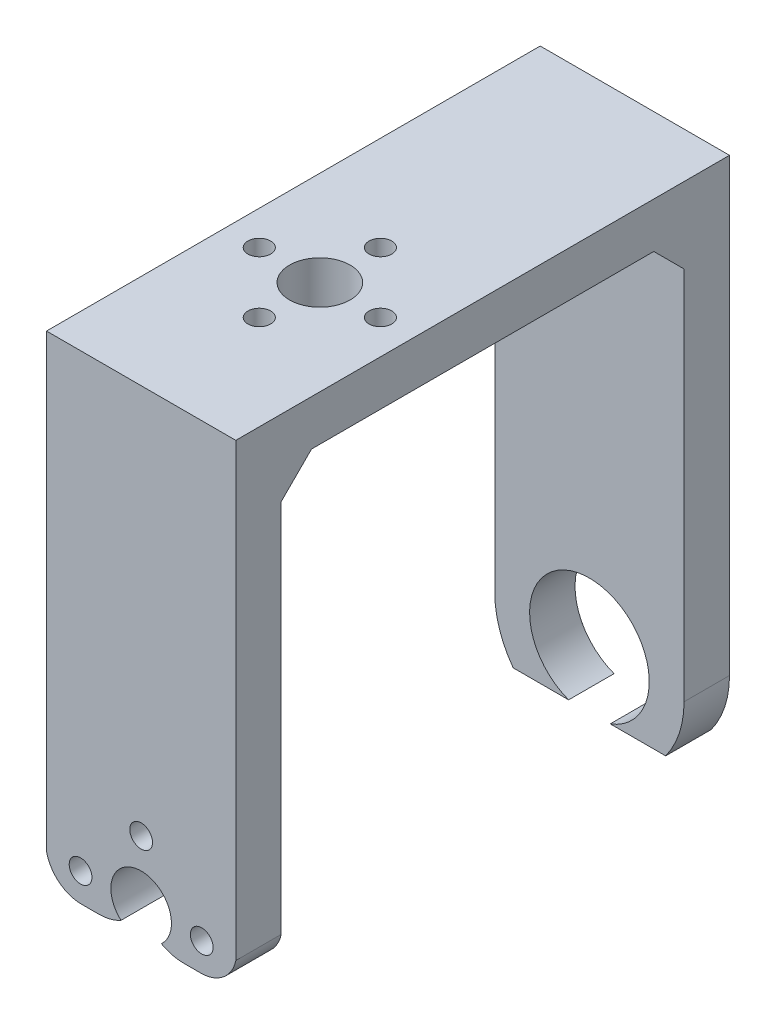
SolidWorks part; units mm, degrees
ref_plane "Alzado" through (0, 0, 0) normal (0, 0, 1) x (1, 0, 0)
ref_plane "Planta" through (0, 0, 0) normal (0, 1, 0) x (1, 0, 0)
ref_plane "Vista lateral" through (0, 0, 0) normal (1, 0, 0) x (0, 0, -1)
sketch "Croquis1" plane through (0, 0, 0) normal (1, 0, 0) x (0, 0, -1)
  line L0 (0, 49.6664) -> (0, -20.3336) construction
  line L1 (-26.6, -20.3336) -> (-26.6, 43.6664)
  line L2 (-26.6, 43.6664) -> (26.6, 43.6664)
  line L3 (-26.6, -20.3336) -> (-32.6, -20.3336)
  line L4 (-32.6, -20.3336) -> (-32.6, 49.6664)
  line L5 (-32.6, 49.6664) -> (32.6, 49.6664)
  line L6 (32.6, -20.3336) -> (32.6, 49.6664)
  line L7 (26.6, -20.3336) -> (32.6, -20.3336)
  line L8 (26.6, -20.3336) -> (26.6, 43.6664)
  point P9 (0, 43.6664)
  dimension "D1" = 53.2
  dimension "D2" = 6
  dimension "D3" = 6
  dimension "D4" = 70
extrude "Saliente-Extruir1" add sketch "Croquis1" along normal blind 25
sketch "Croquis3" plane through (0, 0, -32.6) normal (0, 0, -1) x (-1, 0, 0)
  line L0 (-12.5, -20.3336) -> (-12.5, 7.9911) construction
  line L1 (-25, -20.3336) -> (0, -20.3336) construction
  line L2 (-15.2463, -17.2409) -> (-22.5689, -17.2409)
  line L3 (-25, -20.3336) -> (-25, 49.6664) construction
  line L4 (-25, -9.8336) -> (-25, -20.3336)
  line L5 (-25, -20.3336) -> (0, -20.3336)
  line L6 (0, -9.8336) -> (0, -20.3336)
  line L7 (-9.7537, -17.2409) -> (-2.4311, -17.2409)
  arc A0 (-15.2463, -17.2409) -> (-9.7537, -17.2409) centre (-12.5, -9.8336) cw
  arc A1 (-22.5689, -17.2409) -> (-25, -9.8336) centre (-12.5, -9.8336) cw
  arc A2 (-2.4311, -17.2409) -> (0, -9.8336) centre (-12.5, -9.8336) ccw
  dimension "D2" = 7.9
  dimension "D1" = 10.5
extrude "Cortar-Extruir2" cut sketch "Croquis3" against normal up to next
sketch "Croquis4" plane through (0, 49.6664, 0) normal (0, 1, 0) x (1, 0, 0)
  line L0 (12.5, 32.6) -> (12.5, -32.6) construction
  line L1 (25, 32.6) -> (0, 32.6) construction
  line L2 (25, -32.6) -> (0, -32.6) construction
  line L3 (0, -9) -> (25, -9) construction
  circle A0 centre (12.5, -1) radius 1.5
  circle A1 centre (4.5, -9) radius 1.5
  circle A2 centre (12.5, -17) radius 1.5
  circle A3 centre (20.5, -9) radius 1.5
  circle A4 centre (12.5, -9) radius 4
  point P9 (12.5, 0)
  point P11 (0, 0)
  dimension "D1" = 9
  dimension "D3" = 3
  dimension "D5" = 8
  dimension "D2" = 16
  dimension "D4" = 16
extrude "Cortar-Extruir3" cut sketch "Croquis4" against normal up to next
chamfer "Chaflán1" distance 4 angle 45 2 edges at (12.5, 43.6664, 26.6) (12.5, 43.6664, -26.6)
sketch "Croquis8" plane through (0, 0, 32.6) normal (0, 0, 1) x (1, 0, 0)
  line L0 (12.5, -13.5787) -> (12.5, 49.6664) construction
  line L1 (25, -20.3336) -> (0, -20.3336) construction
  line L2 (25, 49.6664) -> (0, 49.6664) construction
  line L3 (12.5, -9.8336) -> (27.644, -9.8336) construction
  line L4 (4.6051, -13.5787) -> (6.8961, -13.5787)
  line L5 (0, -9.8336) -> (0, -20.3336)
  line L6 (0, -20.3336) -> (25, -20.3336)
  line L7 (25, -20.3336) -> (25, -9.8336)
  line L8 (20.3949, -13.5787) -> (18.1039, -13.5787)
  arc A0 (9.8362, -12.8176) -> (15.1638, -12.8176) centre (12.5, -9.8336) cw
  arc A1 (0, -9.8336) -> (4.6051, -13.5787) centre (4.6051, -8.8749) ccw
  circle A2 centre (4.5, -9.8336) radius 1.5
  circle A3 centre (12.5, -1.8336) radius 1.5
  circle A4 centre (20.5, -9.8336) radius 1.5
  arc A5 (18.1039, -13.5787) -> (15.1638, -12.8176) centre (18.1067, -7.5094) cw
  arc A6 (6.8961, -13.5787) -> (9.8362, -12.8176) centre (6.8933, -7.5094) ccw
  arc A7 (25, -9.8336) -> (20.3949, -13.5787) centre (20.3949, -8.8749) cw
  point P20 (12.5, -9.8336)
  dimension "D1" = 4
  dimension "D3" = 8
  dimension "D5" = 3
  dimension "D2" = 10.5
  dimension "D4" = 8
  dimension "D6" = 8
extrude "Cortar-Extruir5" cut sketch "Croquis8" against normal up to next
